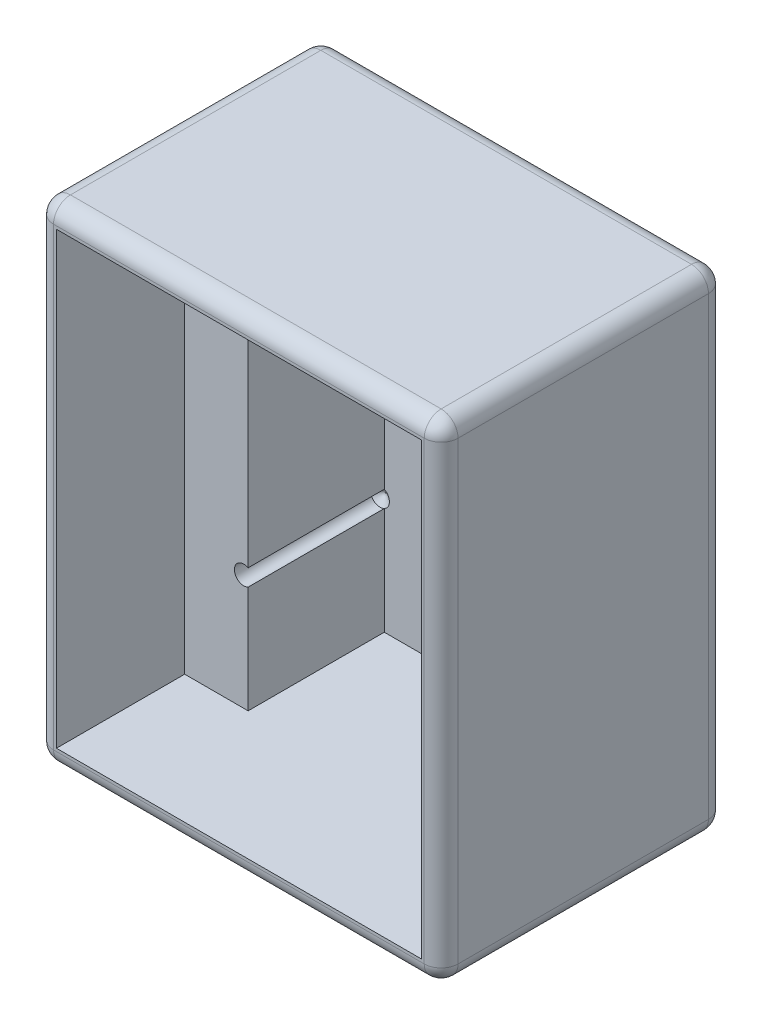
SolidWorks part; units mm, degrees
ref_plane "Front Plane" through (0, 0, 0) normal (0, 0, 1) x (1, 0, 0)
ref_plane "Top Plane" through (0, 0, 0) normal (0, 1, 0) x (1, 0, 0)
ref_plane "Right Plane" through (0, 0, 0) normal (1, 0, 0) x (0, 0, -1)
sketch "Sketch1" plane through (0, 0, 0) normal (0, 0, 1) x (1, 0, 0)
  line L0 (24.2888, 0) -> (24.2888, -58.7375)
  line L1 (24.2888, 0) -> (-24.2888, 0)
  line L2 (0, 0) -> (0, -58.7375)
  line L3 (24.2888, -58.7375) -> (-24.2888, -58.7375)
  line L4 (-24.2888, 0) -> (-24.2888, -58.7375)
extrude "Boss-Extrude1" add sketch "Sketch1" along normal blind 34.1313 contours L1 L4 L3 L0
sketch "Sketch2" plane through (0, 0, 34.1313) normal (0, 0, 1) x (1, 0, 0)
  line L0 (21.9075, -2.3812) -> (21.9075, -56.3562)
  line L1 (21.9075, -2.3812) -> (-21.9075, -2.3812)
  line L2 (0, -2.3812) -> (0, -56.3562)
  line L3 (21.9075, -56.3562) -> (-21.9075, -56.3562)
  line L4 (-21.9075, -2.3812) -> (-21.9075, -56.3562)
extrude "Cut-Extrude1" cut sketch "Sketch2" against normal blind 2.3813 contours L3 L0 L1 L2 | L1 L4 L3 L2
sketch "Sketch4" plane through (0, 0, 31.75) normal (0, 0, 1) x (1, 0, 0)
  line L0 (21.9075, -2.3812) -> (-21.9075, -2.3812) construction
  line L1 (14.2875, -2.3812) -> (-14.2875, -2.3812)
  line L2 (0, -2.3812) -> (0, -56.3562)
  line L3 (14.2875, -56.3562) -> (-14.2875, -56.3562)
  line L4 (-14.2875, -2.3812) -> (-14.2875, -56.3562)
  line L5 (21.9075, -56.3562) -> (-21.9075, -56.3562) construction
  line L6 (14.2875, -2.3812) -> (14.2875, -56.3562)
  line M5 (-21.9075, -56.3562) -> (21.9075, -56.3562)
  line M7 (21.9075, -2.3812) -> (-21.9075, -2.3812)
extrude "Cut-Extrude2" cut sketch "Sketch4" against normal blind 29.3687 contours L6 L2 M7 M5 | L1 L4 L2 M5
sketch "Sketch5" plane through (0, 0, 31.75) normal (0, 0, 1) x (1, 0, 0)
  line L1 (-21.9075, -2.3812) -> (-14.2875, -2.3812)
  line L2 (-21.9075, -2.3812) -> (-21.9075, -56.3562)
  line L3 (-21.9075, -56.3562) -> (-14.2875, -56.3562)
  line L4 (-14.2875, -2.3812) -> (-14.2875, -56.3562)
  line L5 (14.2875, -2.3812) -> (21.9075, -2.3812)
  line L6 (14.2875, -2.3812) -> (14.2875, -56.3562)
  line L7 (14.2875, -56.3562) -> (21.9075, -56.3562)
  line L8 (21.9075, -2.3812) -> (21.9075, -56.3562)
extrude "Cut-Extrude3" cut sketch "Sketch5" against normal blind 13.0175 contours L2 L1 L4 L3 | L6 L5 L8 L7
hole_wizard "#4-40 Tapped Hole1" positions "Sketch8" profile "Sketch9" tap size "#4-40" standard "ANSI Inch"
sketch "Sketch8" plane through (0, 0, 18.7325) normal (0, 0, 1) x (1, 0, 0)
  point P0 (-14.8082, -16.2521)
  point P2 (-14.8082, -42.4854)
  point P4 (14.8082, -42.4854)
  point P6 (14.8082, -16.2521)
  point P14 (0, 0)
  point P15 (0, 0)
  point P16 (0, 0)
  point P17 (0, 0)
  point P18 (0, 0)
  point P19 (0, 0)
  point P20 (0, 0)
  point P21 (0, 0)
  point P22 (0, 0)
sketch "Sketch9" plane through (-14.8082, -16.2521, 18.7325) normal (1, 0, 0) x (0, -1, 0)
  line L0 (0, 0) -> (0, 17.0304)
  line L1 (0, 17.0304) -> (1.1303, 16.3513)
  line L2 (1.1303, 16.3513) -> (1.1303, 0)
  line L5 (1.1303, 0) -> (0, 0)
  line L10 (0, 17.0304) -> (-1.1303, 16.3513) construction
  line L11 (0, -6.35) -> (0, 107.95) construction
  dimension "Tap Drill Dia." = 2.2606
  dimension "Tap Drill Depth" = 16.3513
  dimension "Drill Angle" = 118
cosmetic thread "Hole Thread2" parameters "D1"=5.588, "D2"=2.8448
cosmetic thread "Hole Thread3" parameters "D1"=5.588, "D2"=2.8448
cosmetic thread "Hole Thread4" parameters "D1"=5.588, "D2"=2.8448
cosmetic thread "Hole Thread5" parameters "D1"=5.588, "D2"=2.8448
fillet "Fillet3" radius 2.032 1 edges at (-24.2888, -29.3687, 34.1313)
fillet "Fillet4" radius 2.032 13 edges at (-23.6936, -58.7375, 33.5361) (-23.6936, 0, 33.5361) (-24.2888, -58.7375, 16.0496) (-24.2888, 0, 16.0496) (-24.2888, -29.3687, 0) (0, 0, 0) (0, -58.7375, 0) (24.2888, -58.7375, 17.0656) (24.2888, -29.3687, 0) (24.2888, 0, 17.0656) (1.016, -58.7375, 34.1313) (24.2888, -29.3687, 34.1313) (1.016, 0, 34.1313)
